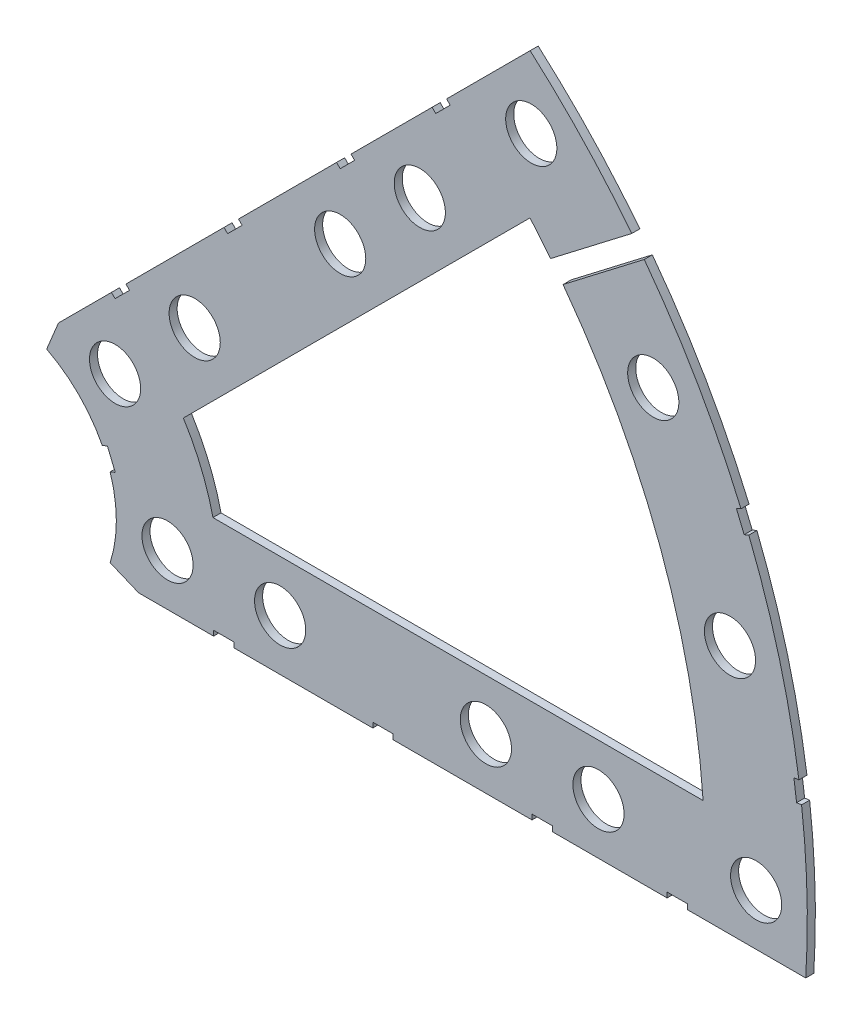
SolidWorks part; units mm, degrees
material "Copper"
ref_plane "Front Plane" through (0, 0, 0) normal (0, 0, 1) x (1, 0, 0)
ref_plane "Top Plane" through (0, 0, 0) normal (0, 1, 0) x (1, 0, 0)
ref_plane "Right Plane" through (0, 0, 0) normal (1, 0, 0) x (0, 0, -1)
sketch "Sketch1" plane through (0, 0, 0) normal (0, 0, 1) x (1, 0, 0)
  line L0 (0, 0) -> (320.3893, 0) construction
  line L1 (0, 0) -> (155.5285, 155.5285) construction
  line L2 (67.2115, 76.1917) -> (8.6967, 17.6769)
  line L3 (8.6967, 17.6769) -> (7.229, 14.1336)
  line L4 (101.4014, -6.35) -> (18.6489, -6.35)
  line L5 (15.1056, -4.8823) -> (18.6489, -6.35)
  line L6 (88.6729, 6.35) -> (27.8605, 6.35)
  line L9 (67.1914, 58.2111) -> (24.1905, 15.2102)
  line L10 (0, 0) -> (40.4486, 97.6516) construction
  line L11 (0, 0) -> (123.4567, -51.1374) construction
  line L18 (8.6967, 17.6769) -> (13.294, 8.6183) construction
  line L19 (18.6489, -6.35) -> (15.4943, 3.3063) construction
  line L20 (27.8605, 6.35) -> (27.7442, 6.7059) construction
  line L21 (24.1905, 15.2102) -> (24.3599, 14.8764) construction
  arc A0 (7.229, 14.1336) -> (15.1056, -4.8823) centre (0, 0) cw
  arc A1 (67.2115, 76.1917) -> (101.4014, -6.35) centre (0, 0) cw
  arc A2 (24.1905, 15.2102) -> (27.8605, 6.35) centre (0, 0) cw
  arc A3 (67.1914, 58.2111) -> (88.6729, 6.35) centre (0, 0) cw
  arc A8 (13.294, 8.6183) -> (15.4943, 3.3063) centre (0, 0) cw construction
  arc A9 (24.3599, 14.8764) -> (27.7442, 6.7059) centre (0, 0) cw construction
  dimension "D1" = 45
  dimension "D3" = 6.35
  dimension "D4" = 15.875
  dimension "D7" = 22.5
  dimension "D8" = 101.6
  dimension "D11" = 12.7
  dimension "D12" = 12.7
  dimension "D2" = 6.35
  dimension "D5" = 67.5
  dimension "D9" = 1.27
  dimension "D10" = 1.27
  dimension "D6" = 12.7
extrude "Boss-Extrude1" add sketch "Sketch1" along normal blind 1
sketch "Sketch2" plane through (0, 0, 1) normal (0, 0, 1) x (1, 0, 0)
  line L0 (0, 0) -> (101.6, 0) construction
  line L1 (0, 0) -> (71.842, 71.842) construction
  line L3 (0, 0) -> (22.225, 0) construction
  line L4 (0, 0) -> (15.7154, 15.7154) construction
  line L5 (0, 0) -> (95.25, 0) construction
  line L6 (0, 0) -> (92.0044, 24.6525) construction
  arc A0 (101.4014, -6.35) -> (67.2115, 76.1917) centre (0, 0) ccw construction
  circle A1 centre (22.225, 0) radius 3.175
  arc A2 (15.1056, -4.8823) -> (7.229, 14.1336) centre (0, 0) ccw construction
  circle A3 centre (36.195, 0) radius 3.175
  circle A4 centre (61.722, 0) radius 3.175
  circle A5 centre (75.692, 0) radius 3.175
  circle A6 centre (95.25, 0) radius 3.175
  circle A7 centre (15.7154, 15.7154) radius 3.175
  circle A8 centre (25.5937, 25.5937) radius 3.175
  circle A9 centre (43.644, 43.644) radius 3.175
  circle A10 centre (53.5223, 53.5223) radius 3.175
  circle A11 centre (92.0044, 24.6525) radius 3.175
  circle A12 centre (82.4889, 47.625) radius 3.175
  circle A13 centre (67.3519, 67.3519) radius 3.175
  dimension "D3" = 6.35
  dimension "D1" = 45
  dimension "D2" = 6.35
  dimension "D4" = 6.35
  dimension "D5" = 13.97
  dimension "D7" = 13.97
  dimension "D8" = 19.558
  dimension "D9" = 45
  dimension "D10" = 15
  dimension "D11" = 25.527
  dimension "D6" = 2
extrude "Cut-Extrude1" cut sketch "Sketch2" against normal through all
sketch "Sketch3" plane through (0, 0, 1) normal (0, 0, 1) x (1, 0, 0)
  line L0 (15.2664, 24.2467) -> (17.0625, 26.0427)
  line L1 (15.2664, 24.2467) -> (15.7154, 23.7977)
  line L2 (17.0625, 26.0427) -> (17.5115, 25.5937)
  line L3 (15.7154, 23.7977) -> (17.5115, 25.5937)
  line L4 (67.2115, 76.1917) -> (8.6967, 17.6769) construction
  line L5 (44.9911, 53.9713) -> (43.195, 52.1753)
  line L6 (44.9911, 53.9713) -> (45.4401, 53.5223)
  line L7 (43.195, 52.1753) -> (43.644, 51.7263)
  line L8 (45.4401, 53.5223) -> (43.644, 51.7263)
  line L9 (27.94, -6.35) -> (30.48, -6.35)
  line L10 (27.94, -6.35) -> (27.94, -5.715)
  line L11 (30.48, -6.35) -> (30.48, -5.715)
  line L12 (27.94, -5.715) -> (30.48, -5.715)
  line L13 (18.6489, -6.35) -> (101.4014, -6.35) construction
  line L14 (67.437, -6.35) -> (69.977, -6.35)
  line L15 (67.437, -6.35) -> (67.437, -5.715)
  line L16 (69.977, -6.35) -> (69.977, -5.715)
  line L17 (67.437, -5.715) -> (69.977, -5.715)
  line L18 (29.2307, 38.211) -> (31.0268, 40.007)
  line L19 (29.2307, 38.211) -> (29.6797, 37.762)
  line L20 (31.0268, 40.007) -> (31.4758, 39.558)
  line L21 (29.6797, 37.762) -> (31.4758, 39.558)
  line L22 (56.845, 65.8253) -> (55.049, 64.0292)
  line L23 (56.845, 65.8253) -> (57.294, 65.3763)
  line L24 (55.049, 64.0292) -> (55.498, 63.5802)
  line L25 (57.294, 65.3763) -> (55.498, 63.5802)
  line L26 (47.6885, -6.35) -> (50.2285, -6.35)
  line L27 (47.6885, -6.35) -> (47.6885, -5.715)
  line L28 (50.2285, -6.35) -> (50.2285, -5.715)
  line L29 (47.6885, -5.715) -> (50.2285, -5.715)
  line L30 (84.201, -6.35) -> (86.741, -6.35)
  line L31 (84.201, -6.35) -> (84.201, -5.715)
  line L32 (86.741, -6.35) -> (86.741, -5.715)
  line L33 (84.201, -5.715) -> (86.741, -5.715)
  line L34 (0, 0) -> (100.7308, 13.2615) construction
  line L35 (0, 0) -> (93.8662, 38.8806) construction
  line L36 (0, 0) -> (80.6047, 61.8502) construction
  line L37 (0, 0) -> (101.6, 0) construction
  line L38 (99.9355, 14.4377) -> (100.267, 11.9194)
  line L39 (99.9355, 14.4377) -> (101.1946, 14.6035)
  line L40 (100.267, 11.9194) -> (101.5261, 12.0852)
  line L41 (101.1946, 14.6035) -> (101.5261, 12.0852)
  line L42 (99.9355, 14.4377) -> (101.5261, 12.0852) construction
  line L43 (100.267, 11.9194) -> (101.1946, 14.6035) construction
  line L44 (93.7655, 37.4643) -> (94.9388, 37.9503)
  line L45 (93.7655, 37.4643) -> (92.7935, 39.811)
  line L46 (94.9388, 37.9503) -> (93.9668, 40.297)
  line L47 (92.7935, 39.811) -> (93.9668, 40.297)
  line L48 (93.7655, 37.4643) -> (93.9668, 40.297) construction
  line L49 (94.9388, 37.9503) -> (92.7935, 39.811) construction
  line L50 (80.8391, 63.6308) -> (82.3854, 61.6157)
  line L51 (80.8391, 63.6308) -> (68.7484, 54.3533)
  line L52 (82.3854, 61.6157) -> (70.2947, 52.3382)
  line L53 (68.7484, 54.3533) -> (70.2947, 52.3382)
  line L56 (13.5939, 7.0054) -> (14.5659, 4.6588)
  line L57 (13.5939, 7.0054) -> (14.7672, 7.4914)
  line L58 (14.5659, 4.6588) -> (15.7393, 5.1448)
  line L59 (14.7672, 7.4914) -> (15.7393, 5.1448)
  line L60 (13.5939, 7.0054) -> (15.7393, 5.1448) construction
  line L61 (14.5659, 4.6588) -> (14.7672, 7.4914) construction
  circle A0 centre (15.7154, 15.7154) radius 3.175 construction
  circle A1 centre (43.644, 43.644) radius 3.175 construction
  circle A2 centre (22.225, 0) radius 3.175 construction
  circle A3 centre (61.722, 0) radius 3.175 construction
  arc A4 (101.4014, -6.35) -> (67.2115, 76.1917) centre (0, 0) ccw construction
  arc A9 (15.1056, -4.8823) -> (7.229, 14.1336) centre (0, 0) ccw construction
  circle A10 centre (36.195, 0) radius 3.175 construction
  circle A11 centre (75.692, 0) radius 3.175 construction
  circle A12 centre (25.5937, 25.5937) radius 3.175 construction
  circle A13 centre (53.5223, 53.5223) radius 3.175 construction
  point P75 (14.6666, 6.0751)
  dimension "D2" = 5.715
  dimension "D3" = 2.54
  dimension "D6" = 5.715
  dimension "D8" = 0.635
  dimension "D9" = 5.715
  dimension "D12" = 5.715
  dimension "D4" = 7.5
  dimension "D5" = 22.5
  dimension "D7" = 37.5
  dimension "D10" = 90
  dimension "D11" = 1.27
  dimension "D14" = 0.635
  dimension "D15" = 90
  dimension "D18" = 0.635
  dimension "D20" = 1.27
  dimension "D17" = 0.635
  dimension "D19" = 15.24
  dimension "D22" = 2.54
  dimension "D21" = 1.27
  dimension "D25" = 1.27
  dimension "D13" = 11.4935
  dimension "D16" = 8.509
  dimension "D23" = 11.4935
  dimension "D24" = 8.509
extrude "Cut-Extrude2" cut sketch "Sketch3" against normal through all
equation "\"cSep\"= 1.005"
equation "\"D11@Sketch2\"=\"cSep\""
equation "\"cSep2\"= \"D8@Sketch2\""
equation "\"D13@Sketch3\"=\"cSep\"/2-.05"
equation "\"D16@Sketch3\"=\"cSep2\"/2-.05"
equation "\"D23@Sketch3\"=\"cSep\"/2-.05"
equation "\"D24@Sketch3\"=\"cSep2\"/2-.05"
